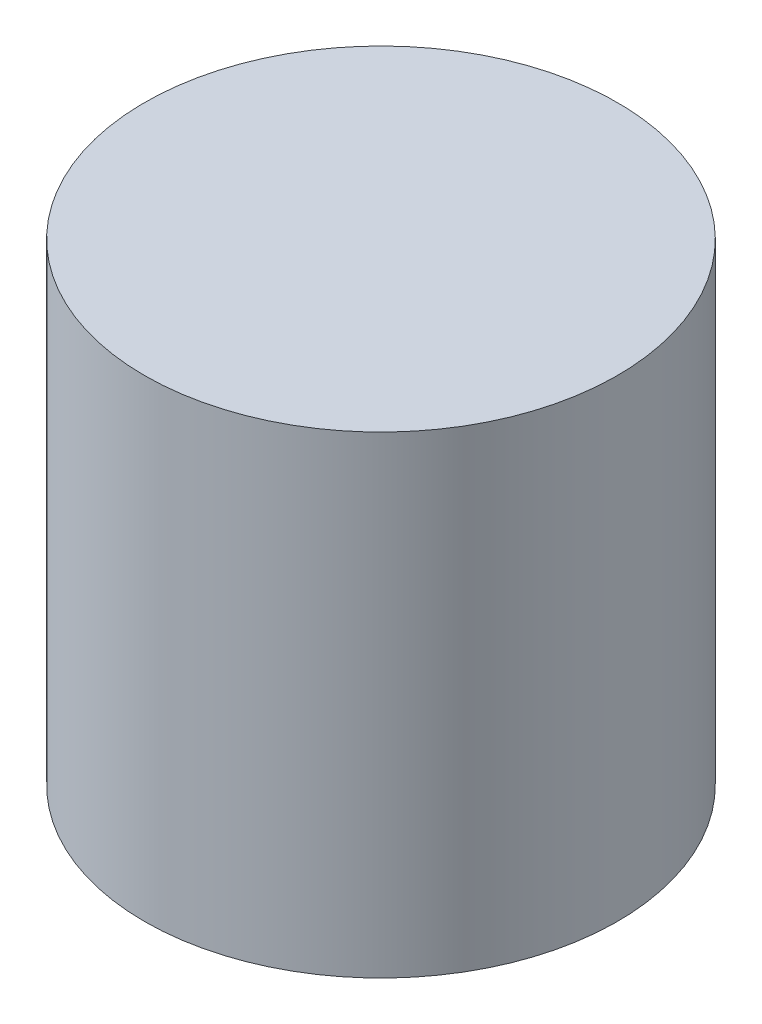
SolidWorks part; units mm, degrees
material "6061-T6 (SS)"
ref_plane "Alzado" through (0, 0, 0) normal (0, 0, 1) x (1, 0, 0)
ref_plane "Planta" through (0, 0, 0) normal (0, 1, 0) x (1, 0, 0)
ref_plane "Vista lateral" through (0, 0, 0) normal (1, 0, 0) x (0, 0, -1)
sketch "Croquis1" plane through (0, 0, 0) normal (0, 1, 0) x (1, 0, 0)
  circle A0 centre (0, 0) radius 3
  dimension "D1" = 6
extrude "Saliente-Extruir1" add sketch "Croquis1" along normal blind 6
